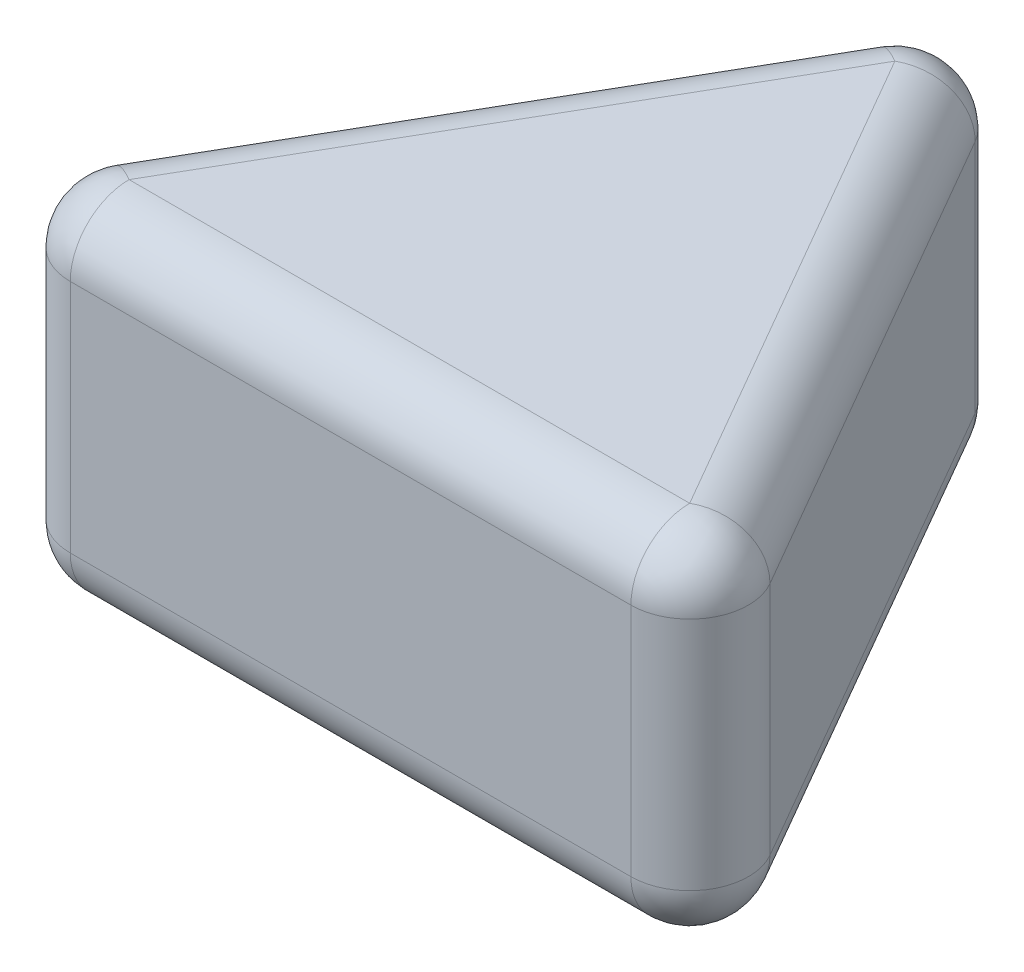
SolidWorks part; units mm, degrees
ref_plane "Front Plane" through (0, 0, 0) normal (0, 0, 1) x (1, 0, 0)
ref_plane "Top Plane" through (0, 0, 0) normal (0, 1, 0) x (1, 0, 0)
ref_plane "Right Plane" through (0, 0, 0) normal (1, 0, 0) x (0, 0, -1)
sketch "Sketch1" plane through (0, 0, 0) normal (0, 1, 0) x (1, 0, 0)
  line L0 (0, 0) -> (6.5, 11.2583)
  line L1 (6.5, 11.2583) -> (13, 0)
  line L2 (13, 0) -> (0, 0)
  dimension "D1" = 13
  dimension "D2" = 13
  dimension "D3" = 13
extrude "Boss-Extrude1" add sketch "Sketch1" along normal blind 6
fillet "Fillet1" radius 1 9 edges at (0, 3, 0) (13, 3, 0) (6.5, 3, -11.2583) (9.75, 0, -5.6292) (3.25, 0, -5.6292) (6.5, 0, 0) (3.25, 6, -5.6292) (9.75, 6, -5.6292) (6.5, 6, 0)
